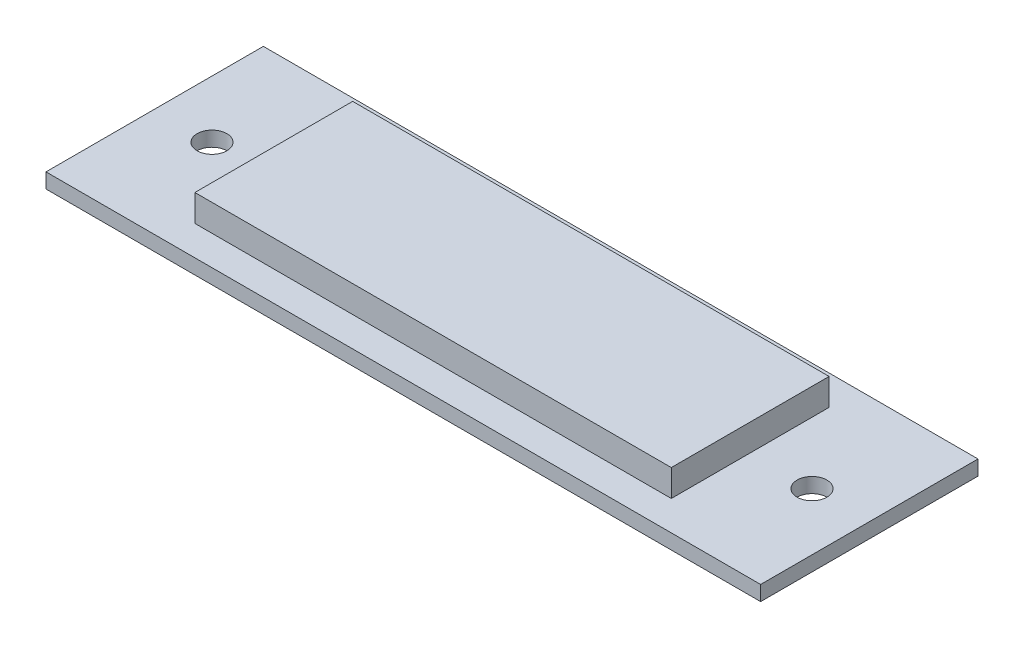
SolidWorks part; units mm, degrees
ref_plane "Front Plane" through (0, 0, 0) normal (0, 0, 1) x (1, 0, 0)
ref_plane "Top Plane" through (0, 0, 0) normal (0, 1, 0) x (1, 0, 0)
ref_plane "Right Plane" through (0, 0, 0) normal (1, 0, 0) x (0, 0, -1)
sketch "Sketch1" plane through (0, 0, 0) normal (0, 1, 0) x (1, 0, 0)
  line L1 (0, 0) -> (80, 0)
  line L2 (0, 0) -> (0, 26.5)
  line L3 (0, 26.5) -> (80, 26.5)
  line L4 (80, 0) -> (80, 26.5)
  dimension "D1" = 80
  dimension "D2" = 26.5
extrude "Boss-Extrude1" add sketch "Sketch1" along normal blind 7
sketch "Sketch5" plane through (0, 0, 0) normal (0, 0, 1) x (1, 0, 0)
  line L0 (80, 0) -> (80, 2.5)
  line L1 (80, 7) -> (80, 0) construction
  line L2 (80, 2.5) -> (0, 2.5)
  line L3 (0, 7) -> (0, 0) construction
  line L4 (0, 2.5) -> (0, 0)
  line L5 (0, 0) -> (80, 0)
extrude "Boss-Extrude5" add sketch "Sketch5" along normal blind 5 and the other way blind 31.5
sketch "Sketch6" plane through (80, 0, 0) normal (1, 0, 0) x (0, 0, -1)
  line L0 (-5, 0) -> (31.5, 0)
  line L1 (31.5, 0) -> (31.5, 2.5)
  line L2 (31.5, 2.5) -> (-5, 2.5)
  line L3 (-5, 2.5) -> (-5, 0)
extrude "Boss-Extrude6" add sketch "Sketch6" along normal blind 20 and the other way blind 100
hole_wizard "Ø5.0mm Dowel Hole1" positions "Sketch11" profile "Sketch10" hole size "Ø5.0" standard "ANSI Metric" end condition through all
sketch "Sketch11" plane through (0, 2.5, 0) normal (0, 1, 0) x (1, 0, 0)
  point P0 (-10.375, 13.25)
  point P3 (90.375, 13.25)
  point P8 (0, 0)
  point P9 (0, 0)
sketch "Sketch10" plane through (-10.375, 2.5, -13.25) normal (1, 0, 0) x (0, 0, 1)
  line L0 (0, 0) -> (0, 2.5)
  line L1 (0, 2.5) -> (2.5, 2.5)
  line L2 (2.5, 2.5) -> (2.5, 0)
  line L5 (2.5, 0) -> (0, 0)
  line L11 (0, -6.35) -> (0, 107.95) construction
  dimension "Thru Hole Dia." = 5
  dimension "Thru Hole Depth" = 2.5
